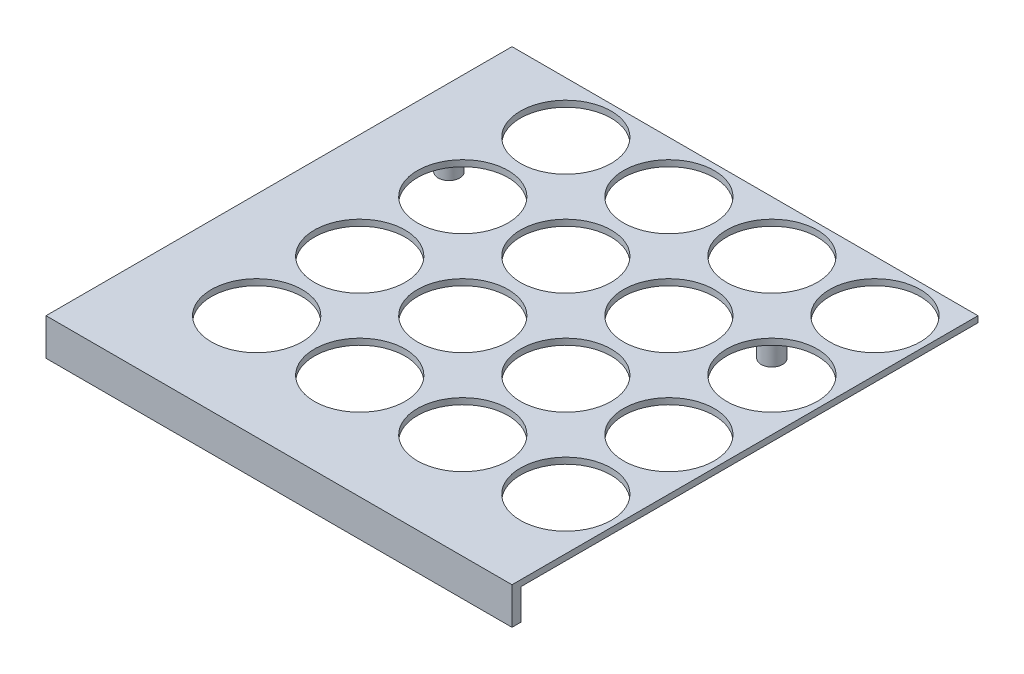
SolidWorks part; units mm, degrees
ref_plane "Front Plane" through (0, 0, 0) normal (0, 0, 1) x (1, 0, 0)
ref_plane "Top Plane" through (0, 0, 0) normal (0, 1, 0) x (1, 0, 0)
ref_plane "Right Plane" through (0, 0, 0) normal (1, 0, 0) x (0, 0, -1)
sketch "Sketch1" plane through (0, 0, 0) normal (0, 1, 0) x (1, 0, 0)
  line L1 (0, 0) -> (151.5, 0)
  line L2 (0, 0) -> (0, 151.5)
  line L3 (0, 151.5) -> (151.5, 151.5)
  line L4 (151.5, 0) -> (151.5, 151.5)
  dimension "D1" = 151.5
  dimension "D2" = 151.5
extrude "Boss-Extrude1" add sketch "Sketch1" along normal blind 2
sketch "Sketch2" plane through (0, 0, 0) normal (0, 1, 0) x (1, 0, 0)
  circle A0 centre (34.25, 34.25) radius 14.75
extrude "Cut-Extrude2" cut sketch "Sketch2" along normal blind 2
pattern_linear "LPattern1" count 4 spacing 33.5 along (1, 0, 0) count 4 spacing 33.5 along (0, 0, -1) of "Cut-Extrude2"
sketch "Sketch3" plane through (0, 0, 0) normal (0, 1, 0) x (1, 0, 0)
  line L1 (0, 151.5) -> (151.5, 151.5)
  line L2 (0, 151.5) -> (0, 0)
  line L3 (0, 0) -> (151.5, 0)
  line L4 (151.5, 151.5) -> (151.5, 0)
extrude "Boss-Extrude2" add sketch "Sketch3" against normal blind 10
sketch "Sketch5" plane through (0, 0, 0) normal (0, 1, 0) x (1, 0, 0)
  line L1 (3, 3) -> (151.5, 3)
  line L2 (3, 3) -> (3, 151.5)
  line L3 (3, 151.5) -> (151.5, 151.5)
  line L4 (151.5, 3) -> (151.5, 151.5)
extrude "Cut-Extrude4" cut sketch "Sketch5" against normal blind 10
sketch "Sketch8" plane through (0, 0, 0) normal (0, 1, 0) x (1, 0, 0)
  circle A0 centre (13, 13) radius 3.5
extrude "Boss-Extrude4" add sketch "Sketch8" against normal blind 10
pattern_linear "LPattern2" count 2 spacing 105 along (0, 0, -1) count 2 spacing 105 along (1, 0, 0) of "Boss-Extrude4"
